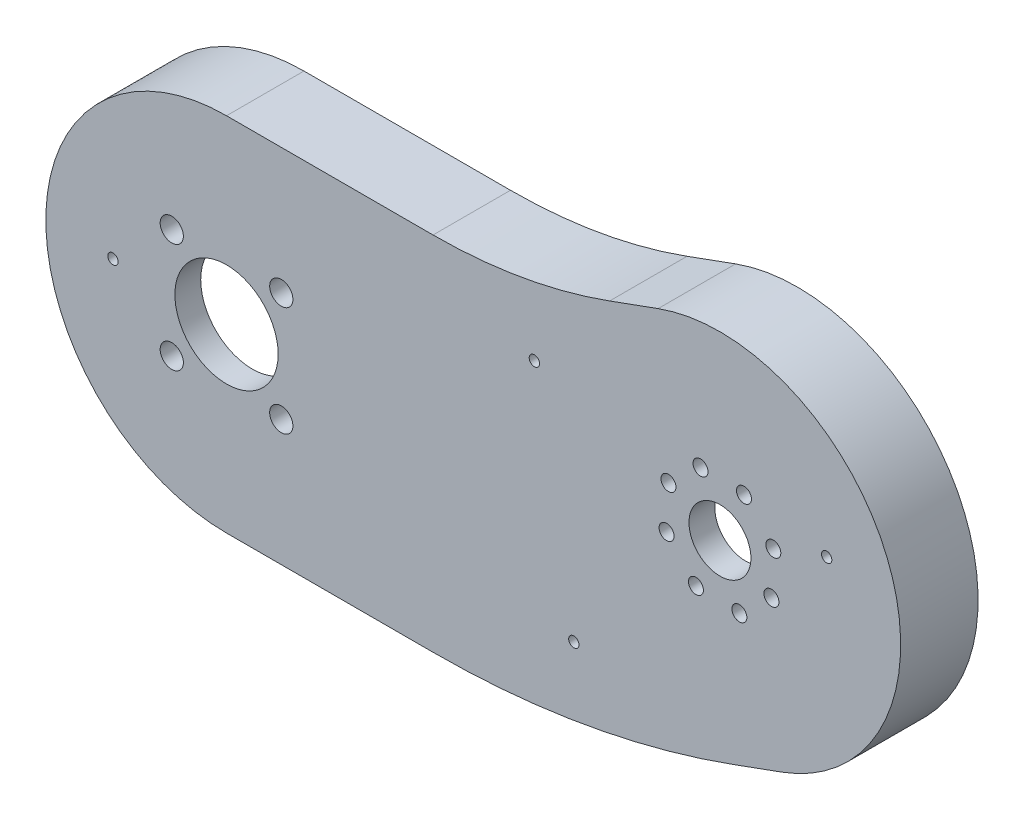
SolidWorks part; units mm, degrees
ref_plane "정면" through (0, 0, 0) normal (0, 0, 1) x (1, 0, 0)
ref_plane "윗면" through (0, 0, 0) normal (0, 1, 0) x (1, 0, 0)
ref_plane "우측면" through (0, 0, 0) normal (1, 0, 0) x (0, 0, -1)
sketch "스케치1" plane through (0, 0, 0) normal (0, 0, 1) x (1, 0, 0)
  line L0 (40, -1088.5095) -> (40, -35) construction
  line L1 (0, 35) -> (40, 35)
  line L3 (0, -35) -> (40, -35)
  line L6 (40, 135) -> (40, 50018.5095) construction
  line L7 (74.202, 41.0307) -> (83.5989, 44.4509)
  line L9 (107.5404, -21.3275) -> (98.1434, -24.7477)
  arc A0 (0, 35) -> (0, -35) centre (0, 0) ccw
  arc A1 (40, 35) -> (74.202, 41.0307) centre (40, 135) ccw
  arc A3 (40, -35) -> (98.1434, -24.7477) centre (40, 135) ccw
  arc A4 (107.5404, -21.3275) -> (83.5989, 44.4509) centre (95.5696, 11.5617) ccw
  point P7 (40, 135)
  dimension "D1" = 70
  dimension "D4" = 200
  dimension "D5" = 10
  dimension "D7" = 70
  dimension "D2" = 40
  dimension "D3" = 100
extrude "보스-돌출1" add sketch "스케치1" along normal blind 20
chamfer "모따기1" distance 10 angle 45 8 edges at (20, -35, 0) (69.5202, -32.4173, 0) (102.8419, -23.0376, 0) (128.4589, 23.5324, 0) (78.9005, 42.7408, 0) (57.3648, 36.5192, 0) (20, 35, 0) (-35, 0, 0)
sketch "스케치2" plane through (0, 0, 0) normal (0, 0, -1) x (-1, 0, 0)
  line L8 (-40, -25) -> (0, -25)
  line L9 (0, 25) -> (-40, 25)
  line L10 (-77.6222, 31.6338) -> (-87.0191, 35.054)
  line L11 (-104.1201, -11.9306) -> (-94.7232, -15.3508)
  line L12 (-40, -25) -> (0, -25)
  line L13 (0, 25) -> (-40, 25)
  line L14 (-77.6222, 31.6338) -> (-87.0191, 35.054)
  line L15 (-104.1201, -11.9306) -> (-94.7232, -15.3508)
  arc A8 (-94.7232, -15.3508) -> (-40, -25) centre (-40, 135) ccw
  arc A9 (0, -25) -> (0, 25) centre (0, 0) ccw
  arc A10 (-77.6222, 31.6338) -> (-40, 25) centre (-40, 135) ccw
  arc A11 (-87.0191, 35.054) -> (-104.1201, -11.9306) centre (-95.5696, 11.5617) ccw
  arc A12 (-94.7232, -15.3508) -> (-40, -25) centre (-40, 135) ccw
  arc A13 (0, -25) -> (0, 25) centre (0, 0) ccw
  arc A14 (-77.6222, 31.6338) -> (-40, 25) centre (-40, 135) ccw
  arc A15 (-87.0191, 35.054) -> (-104.1201, -11.9306) centre (-95.5696, 11.5617) ccw
  dimension "D1" = 0
extrude "컷-돌출1" cut sketch "스케치2" against normal blind 15
sketch "스케치3" plane through (0, 0, 20) normal (0, 0, 1) x (1, 0, 0)
  line L0 (85.309, 39.7525) -> (17186.3162, -46944.8786) construction
  line L1 (87.0191, 35.054) -> (83.5989, 44.4509) construction
  line L2 (95.5696, 11.5617) -> (47080.2007, 17112.5689) construction
  line L3 (95.5696, 11.5617) -> (45410.959, -21119.3514) construction
  line L4 (95.5696, 11.5617) -> (21226.4827, 45326.951) construction
  circle A0 centre (95.5696, 11.5617) radius 15 construction
  circle A1 centre (105.9063, 15.3239) radius 1.45
  circle A2 centre (95.5696, 11.5617) radius 6
  circle A3 centre (91.8074, 21.8983) radius 1.45
  circle A4 centre (85.233, 7.7995) radius 1.45
  circle A5 centre (99.3319, 1.2251) radius 1.45
  circle A6 centre (85.6003, 16.2105) radius 1.45
  circle A7 centre (100.2184, 21.5311) radius 1.45
  circle A8 centre (105.539, 6.9129) radius 1.45
  circle A9 centre (90.9208, 1.5923) radius 1.45
  point P4 (85.309, 39.7525)
  point P7 (56.7337, 48.9453)
  point P8 (83.5989, 44.4509)
  dimension "D1" = 30
  dimension "D3" = 2.9
  dimension "D5" = 2.9
  dimension "D6" = 2.9
  dimension "D7" = 2.9
  dimension "D11" = 12
  dimension "D14" = 2.9
  dimension "D15" = 2.9
  dimension "D16" = 2.9
  dimension "D17" = 2.9
  dimension "D2" = 35
  dimension "D4" = 11
  dimension "D8" = 11
  dimension "D9" = 11
  dimension "D10" = 11
  dimension "D12" = 45
  dimension "D13" = 45
  dimension "D18" = 11
  dimension "D19" = 11
  dimension "D20" = 11
  dimension "D21" = 11
extrude "컷-돌출2" cut sketch "스케치3" against normal up to next
sketch "스케치4" plane through (0, 0, 20) normal (0, 0, 1) x (1, 0, 0)
  line L0 (0, 27.384) -> (0, -49972.616) construction
  line L1 (0, 0) -> (35355.3391, 35355.3391) construction
  line L2 (0, -35) -> (0, -25) construction
  line L3 (0, 0) -> (50000, 0) construction
  line L4 (0, 0) -> (-35355.3391, 35355.3391) construction
  circle A0 centre (0, 0) radius 10
  circle A1 centre (0, 0) radius 15 construction
  circle A2 centre (10.6066, -10.6066) radius 2.25
  circle A3 centre (10.6066, 10.6066) radius 2.25
  circle A4 centre (-10.6066, -10.6066) radius 2.25
  circle A5 centre (-10.6066, 10.6066) radius 2.25
  point P6 (0, -30)
  point P8 (0, 35)
  dimension "D1" = 20
  dimension "D2" = 30
  dimension "D3" = 4.5
  dimension "D4" = 4.5
  dimension "D5" = 4.5
  dimension "D6" = 4.5
  dimension "D7" = 45
  dimension "D8" = 45
extrude "컷-돌출3" cut sketch "스케치4" against normal up to next
sketch "스케치5" plane through (0, 0, 15) normal (0, 0, -1) x (-1, 0, 0)
  line L0 (0, 27.4907) -> (0, 50027.4907) construction
  line L2 (-75.9121, 36.3323) -> (-17176.9193, -46948.2988) construction
  line L4 (-86.1766, 8.131) -> (-47051.6074, 17161.7984) construction
  line L5 (0, 0) -> (50000, 0) construction
  line L6 (-74.202, 41.0307) -> (-77.6222, 31.6338) construction
  line L9 (-40, 30) -> (-40, -49970) construction
  line L10 (-40, 35) -> (-40, 25) construction
  line L11 (-40, 135) -> (-8722.4089, -49105.3877) construction
  arc A0 (-74.202, 41.0307) -> (-40, 35) centre (-40, 135) ccw construction
  circle A1 centre (22, 0) radius 4
  circle A2 centre (-59.6222, 23.7167) radius 4
  circle A3 centre (-67.2628, -19.6148) radius 4
  circle A4 centre (-116.2345, 19.1094) radius 4
  arc A5 (0, -25) -> (0, 25) centre (0, 0) ccw construction
  arc A6 (-94.7232, -15.3508) -> (-40, -25) centre (-40, 135) ccw construction
  arc A7 (-77.6222, 31.6338) -> (-40, 25) centre (-40, 135) ccw construction
  arc A8 (-87.0191, 35.054) -> (-104.1201, -11.9306) centre (-95.5696, 11.5617) ccw construction
  point P12 (-75.9121, 36.3323)
  point P14 (-63.8041, 0)
  point P18 (-40, 30)
  point P25 (-57.3648, 36.5192)
  point P34 (-67.7837, -22.5692)
  point P35 (-59.1013, 26.6711)
  point P39 (25, 0)
  point P40 (-119.062, 20.1122)
  dimension "D1" = 8
  dimension "D2" = 8
  dimension "D3" = 8
  dimension "D4" = 8
  dimension "D5" = 3
  dimension "D6" = 3
  dimension "D7" = 3
  dimension "D8" = 3
extrude "보스-돌출2" add sketch "스케치5" along normal blind 5
fillet "필렛1" radius 5 8 edges at (65.1496, -23.0111, 12.5) (70.4101, -22.0835, 12.5) (-24.8409, 2.8159, 12.5) (-24.8409, -2.8159, 12.5) (119.869, 17.4388, 12.5) (117.9368, 22.7291, 12.5) (56.5254, 26.2484, 12.5) (61.6665, 27.1549, 12.5)
sketch "스케치6" plane through (0, 0, 10) normal (0, 0, -1) x (-1, 0, 0)
  line L0 (-59.6222, 23.7167) -> (-8742.0311, -49216.6709) construction
  line L1 (-59.6222, 23.7167) -> (49180.7654, -8658.6922) construction
  line L2 (-67.2628, -19.6148) -> (49173.1249, -8702.0237) construction
  line L3 (-116.2345, 19.1094) -> (-8798.6434, -49221.2783) construction
  line L4 (-116.2345, 19.1094) -> (49124.1531, -8663.2995) construction
  line L5 (22, 0) -> (50022, 0) construction
  line L6 (22, 0) -> (22, 50000) construction
  circle A0 centre (-116.2345, 19.1094) radius 1
  circle A1 centre (-67.2628, -19.6148) radius 1
  circle A2 centre (-59.6222, 23.7167) radius 1
  circle A3 centre (22, 0) radius 1
  dimension "D1" = 2
  dimension "D2" = 2
  dimension "D3" = 2
  dimension "D4" = 2
extrude "컷-돌출4" cut sketch "스케치6" against normal up to next
fillet "필렛2" radius 5 8 edges at (102.8419, -23.0376, 10) (69.5202, -32.4173, 10) (20, -35, 10) (-35, 0, 10) (20, 35, 10) (57.3648, 36.5192, 10) (78.9005, 42.7408, 10) (128.4589, 23.5324, 10)
ref_plane "평면1" through (0, 0, 0) normal (0, 0, 1) x (1, 0, 0)
sketch "스케치7" plane through (0, 0, 0) normal (0, 0, 1) x (1, 0, 0)
  line L21 (98.1434, -24.7477) -> (107.5404, -21.3275)
  line L22 (0, -35) -> (40, -35)
  line L23 (40, 35) -> (0, 35)
  line L24 (83.5989, 44.4509) -> (74.202, 41.0307)
  line L25 (98.1434, -24.7477) -> (107.5404, -21.3275)
  line L26 (0, -35) -> (40, -35)
  line L27 (40, 35) -> (0, 35)
  line L28 (83.5989, 44.4509) -> (74.202, 41.0307)
  line L45 (94.7232, -15.3508) -> (104.1201, -11.9306)
  line L46 (0, -25) -> (40, -25)
  line L47 (40, 25) -> (0, 25)
  line L48 (87.0191, 35.054) -> (77.6222, 31.6338)
  line L49 (94.7232, -15.3508) -> (104.1201, -11.9306)
  line L50 (0, -25) -> (40, -25)
  line L51 (40, 25) -> (0, 25)
  line L52 (87.0191, 35.054) -> (77.6222, 31.6338)
  arc A26 (40, -35) -> (98.1434, -24.7477) centre (40, 135) ccw
  arc A27 (0, 35) -> (0, -35) centre (0, 0) ccw
  arc A28 (40, 35) -> (74.202, 41.0307) centre (40, 135) ccw
  arc A29 (107.5404, -21.3275) -> (83.5989, 44.4509) centre (95.5696, 11.5617) ccw
  arc A30 (40, -35) -> (98.1434, -24.7477) centre (40, 135) ccw
  arc A31 (0, 35) -> (0, -35) centre (0, 0) ccw
  arc A32 (40, 35) -> (74.202, 41.0307) centre (40, 135) ccw
  arc A33 (107.5404, -21.3275) -> (83.5989, 44.4509) centre (95.5696, 11.5617) ccw
  arc A54 (40, -25) -> (94.7232, -15.3508) centre (40, 135) ccw
  arc A55 (0, 25) -> (0, -25) centre (0, 0) ccw
  arc A56 (40, 25) -> (77.6222, 31.6338) centre (40, 135) ccw
  arc A57 (104.1201, -11.9306) -> (87.0191, 35.054) centre (95.5696, 11.5617) ccw
  arc A58 (40, -25) -> (94.7232, -15.3508) centre (40, 135) ccw
  arc A59 (0, 25) -> (0, -25) centre (0, 0) ccw
  arc A60 (40, 25) -> (77.6222, 31.6338) centre (40, 135) ccw
  arc A61 (104.1201, -11.9306) -> (87.0191, 35.054) centre (95.5696, 11.5617) ccw
  dimension "D1" = 0
  dimension "D2" = 0
extrude "보스-돌출3" add sketch "스케치7" along normal blind 13
sketch "스케치8" plane through (0, 0, 0) normal (0, 0, -1) x (-1, 0, 0)
  line L8 (-74.202, 41.0307) -> (-83.5989, 44.4509)
  line L9 (-107.5404, -21.3275) -> (-98.1434, -24.7477)
  line L10 (-40, -35) -> (0, -35)
  line L11 (0, 35) -> (-40, 35)
  line L12 (-74.202, 41.0307) -> (-83.5989, 44.4509)
  line L13 (-107.5404, -21.3275) -> (-98.1434, -24.7477)
  line L14 (-40, -35) -> (0, -35)
  line L15 (0, 35) -> (-40, 35)
  line L28 (-104.1201, -11.9306) -> (-94.7232, -15.3508)
  line L29 (-40, -25) -> (0, -25)
  line L30 (0, 25) -> (-40, 25)
  line L31 (-77.6222, 31.6338) -> (-87.0191, 35.054)
  line L32 (-104.1201, -11.9306) -> (-94.7232, -15.3508)
  line L33 (-40, -25) -> (0, -25)
  line L34 (0, 25) -> (-40, 25)
  line L35 (-77.6222, 31.6338) -> (-87.0191, 35.054)
  arc A8 (-74.202, 41.0307) -> (-40, 35) centre (-40, 135) ccw
  arc A9 (-83.5989, 44.4509) -> (-107.5404, -21.3275) centre (-95.5696, 11.5617) ccw
  arc A10 (-98.1434, -24.7477) -> (-40, -35) centre (-40, 135) ccw
  arc A11 (0, -35) -> (0, 35) centre (0, 0) ccw
  arc A12 (-74.202, 41.0307) -> (-40, 35) centre (-40, 135) ccw
  arc A13 (-83.5989, 44.4509) -> (-107.5404, -21.3275) centre (-95.5696, 11.5617) ccw
  arc A14 (-98.1434, -24.7477) -> (-40, -35) centre (-40, 135) ccw
  arc A15 (0, -35) -> (0, 35) centre (0, 0) ccw
  arc A32 (-94.7232, -15.3508) -> (-40, -25) centre (-40, 135) ccw
  arc A33 (0, -25) -> (0, 25) centre (0, 0) ccw
  arc A34 (-77.6222, 31.6338) -> (-40, 25) centre (-40, 135) ccw
  arc A35 (-87.0191, 35.054) -> (-104.1201, -11.9306) centre (-95.5696, 11.5617) ccw
  arc A36 (-94.7232, -15.3508) -> (-40, -25) centre (-40, 135) ccw
  arc A37 (0, -25) -> (0, 25) centre (0, 0) ccw
  arc A38 (-77.6222, 31.6338) -> (-40, 25) centre (-40, 135) ccw
  arc A39 (-87.0191, 35.054) -> (-104.1201, -11.9306) centre (-95.5696, 11.5617) ccw
  dimension "D1" = 0
  dimension "D2" = 0
extrude "컷-돌출5" cut sketch "스케치8" against normal blind 5
